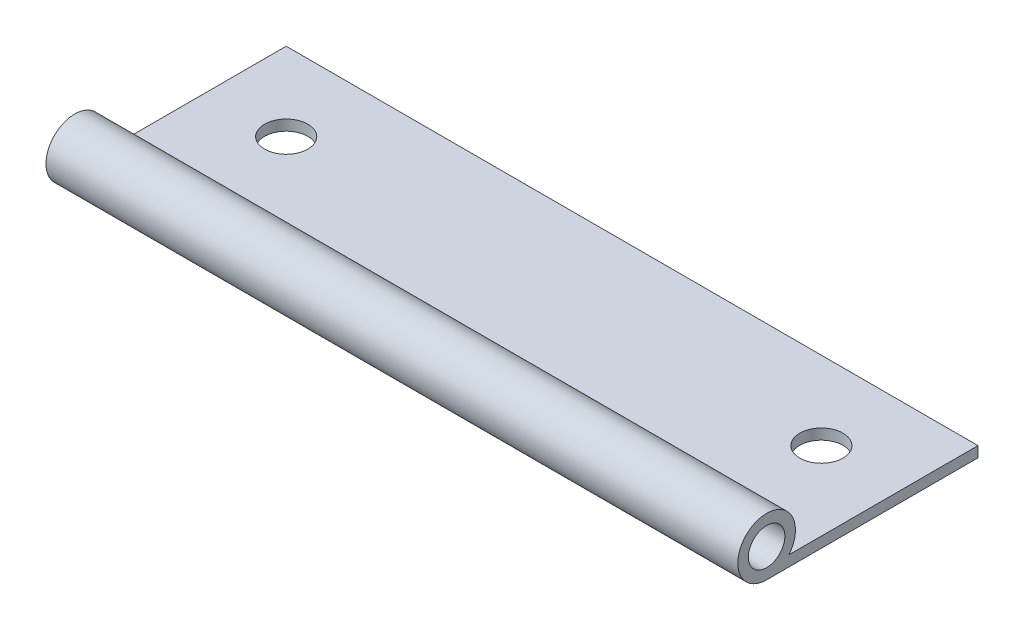
SolidWorks part; units mm, degrees
ref_plane "Front" through (0, 0, 0) normal (0, 0, 1) x (1, 0, 0)
ref_plane "Top" through (0, 0, 0) normal (0, 1, 0) x (1, 0, 0)
ref_plane "Right" through (0, 0, 0) normal (1, 0, 0) x (0, 0, -1)
sketch "草图1" plane through (0, 0, 0) normal (1, 0, 0) x (0, 0, -1)
  line L0 (0, 0) -> (19, 0)
  line L1 (19, 0) -> (19, -1.1)
  line L2 (19, -1.1) -> (0, -1.1)
  line L3 (0, -1.1) -> (0, 5.2282) construction
  line L4 (0, -1.1) -> (-3, -1.1)
  line L5 (0, 0) -> (-0.6784, 0)
  arc A0 (-0.6784, 0) -> (-3, -1.1) centre (-3, 1.9) ccw
  circle A1 centre (-3, 1.9) radius 1.9
  dimension "D3" = 6
  dimension "D1" = 19
  dimension "D2" = 1.1
extrude "凸台-拉伸1" add sketch "草图1" along normal blind 72
sketch "草图2" plane through (0, 0, 0) normal (0, 1, 0) x (1, 0, 0)
  line L0 (0, 10.85) -> (72, 10.85) construction
  line L1 (0, 19) -> (0, -0.6784) construction
  line L2 (72, 19) -> (72, -0.6784) construction
  line L3 (72, 19) -> (0, 19) construction
  line L4 (36, 19) -> (36, -12.902) construction
  circle A0 centre (8.15, 10.85) radius 2.25
  circle A1 centre (63.85, 10.85) radius 2.25
  dimension "D1" = 4.5
  dimension "D2" = 8.15
  dimension "D3" = 8.15
extrude "切除-拉伸1" cut sketch "草图2" against normal through all
